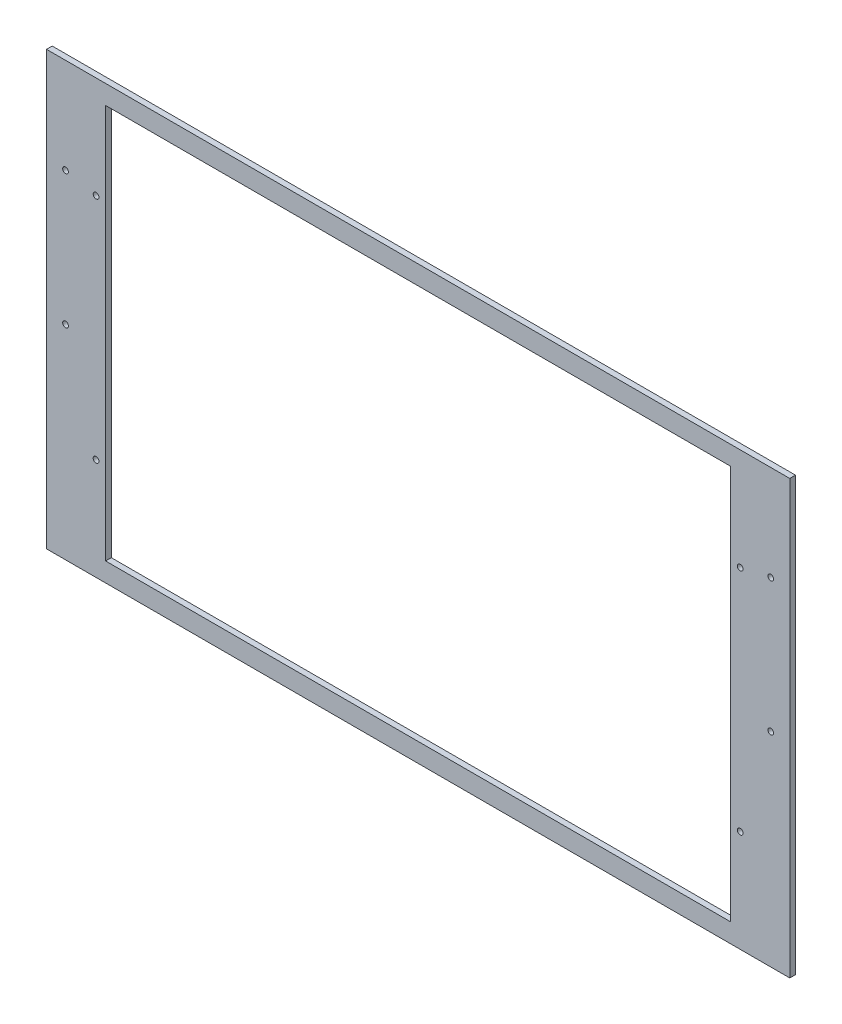
SolidWorks part; units mm, degrees
material "Polywood"
ref_plane "Front Plane" through (0, 0, 0) normal (0, 0, 1) x (1, 0, 0)
ref_plane "Top Plane" through (0, 0, 0) normal (0, 1, 0) x (1, 0, 0)
ref_plane "Right Plane" through (0, 0, 0) normal (1, 0, 0) x (0, 0, -1)
sketch "Sketch1" plane through (0, 0, 0) normal (0, 0, 1) x (1, 0, 0)
  line L1 (-195, 113.5) -> (195, 113.5)
  line L2 (-195, 113.5) -> (-195, -113.5)
  line L3 (-195, -113.5) -> (195, -113.5)
  line L4 (195, 113.5) -> (195, -113.5)
  line L5 (164, -103.5) -> (-164, -103.5)
  line L6 (164, -103.5) -> (164, 103.5)
  line L7 (164, 103.5) -> (-164, 103.5)
  line L8 (-164, -103.5) -> (-164, 103.5)
  line L9 (164, -103.5) -> (-164, 103.5) construction
  line L10 (164, 103.5) -> (-164, -103.5) construction
  point P4 (195, 0)
  point P6 (0, 113.5)
  point P7 (0, 0)
  dimension "D1" = 227
  dimension "D2" = 390
  dimension "D3" = 328
  dimension "207" = 207
extrude "Boss-Extrude1" add sketch "Sketch1" along normal blind 3
sketch "Sketch2" plane through (0, 0, 3) normal (0, 0, 1) x (1, 0, 0)
  line L0 (0, 0) -> (0, -50000) construction
  line L1 (195, 113.5) -> (-195, 113.5) construction
  line L3 (-195, 113.5) -> (-195, -113.5) construction
  line L4 (-176.4155, 28.5) -> (49823.5845, 28.5) construction
  circle A0 centre (-185, 63.5) radius 1.5
  circle A1 centre (-185, -6.5) radius 1.5
  circle A2 centre (185, -6.5) radius 1.5
  circle A3 centre (185, 63.5) radius 1.5
  dimension "D3" = 3
  dimension "D1" = 50
  dimension "D2" = 10
  dimension "D4" = 35
extrude "Cut-Extrude1" cut sketch "Sketch2" against normal through all
sketch "Sketch3" plane through (0, 0, 3) normal (0, 0, 1) x (1, 0, 0)
  line L0 (-164, 0) -> (49836, 0) construction
  line L1 (-164, 103.5) -> (-164, -103.5) construction
  line L2 (0, 0) -> (0, 50000) construction
  circle A0 centre (-169, 60) radius 1.5
  circle A1 centre (-169, -60) radius 1.5
  circle A2 centre (169, -60) radius 1.5
  circle A3 centre (169, 60) radius 1.5
  point P6 (-164, 0)
  dimension "D2" = 3
  dimension "D1" = 60
  dimension "D3" = 5
extrude "Cut-Extrude2" cut sketch "Sketch3" against normal through all
